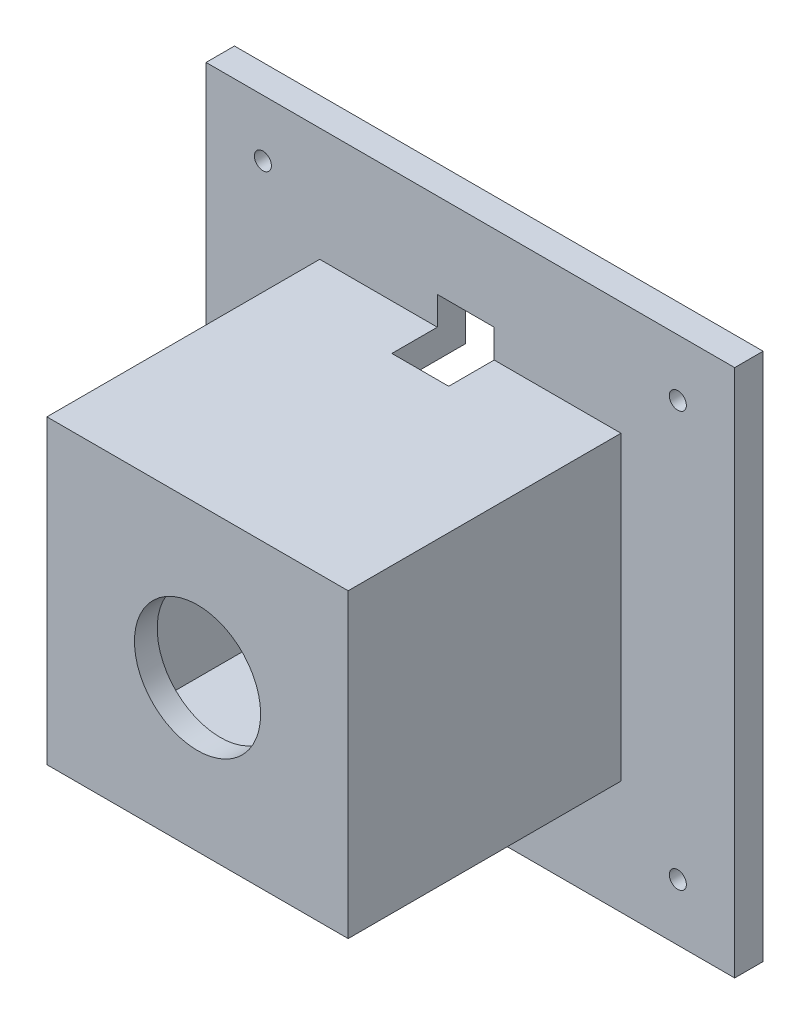
SolidWorks part; units mm, degrees
ref_plane "Plan de face" through (0, 0, 0) normal (0, 0, 1) x (1, 0, 0)
ref_plane "Plan de dessus" through (0, 0, 0) normal (0, 1, 0) x (1, 0, 0)
ref_plane "Plan de droite" through (0, 0, 0) normal (1, 0, 0) x (0, 0, -1)
sketch "Esquisse1" plane through (0, 0, 0) normal (0, 0, 1) x (1, 0, 0)
  line L1 (-21.4803, 20.2237) -> (71.5197, 20.2237)
  line L2 (-21.4803, 20.2237) -> (-21.4803, -72.7763)
  line L3 (-21.4803, -72.7763) -> (71.5197, -72.7763)
  line L4 (71.5197, 20.2237) -> (71.5197, -72.7763)
  dimension "D1" = 93
  dimension "D2" = 93
extrude "Boss.-Extru.1" add sketch "Esquisse1" along normal blind 5
sketch "Esquisse2" plane through (0, 0, 5) normal (0, 0, 1) x (1, 0, 0)
  line L0 (-21.4803, 20.2237) -> (71.5197, -72.7763) construction
  line L1 (71.5197, -72.7763) -> (71.5197, 20.2237) construction
  line L2 (71.5197, 20.2237) -> (-21.4803, -72.7763) construction
  line L4 (-1.4803, 0.2237) -> (51.5197, 0.2237)
  line L5 (-1.4803, 0.2237) -> (-1.4803, -52.7763)
  line L6 (-1.4803, -52.7763) -> (51.5197, -52.7763)
  line L7 (51.5197, 0.2237) -> (51.5197, -52.7763)
  dimension "D1" = 53
  dimension "D2" = 53
extrude "Boss.-Extru.2" add sketch "Esquisse2" along normal blind 48
sketch "Esquisse3" plane through (0, 0, 0) normal (0, 0, -1) x (-1, 0, 0)
  line L8 (21.4803, 20.2237) -> (-71.5197, -72.7763) construction
  line L9 (-46.5197, -47.7763) -> (-3.5197, -47.7763)
  line L10 (-46.5197, -47.7763) -> (-46.5197, -4.7763)
  line L11 (-46.5197, -4.7763) -> (-3.5197, -4.7763)
  line L12 (-3.5197, -47.7763) -> (-3.5197, -4.7763)
  line L13 (-46.5197, -47.7763) -> (-3.5197, -4.7763) construction
  line L14 (-46.5197, -4.7763) -> (-3.5197, -47.7763) construction
  point P0 (-25.0197, -26.2763)
  dimension "D1" = 43
  dimension "D2" = 43
extrude "Enlèv. mat.-Extru.1" cut sketch "Esquisse3" against normal blind 49
sketch "Esquisse4" plane through (0, 0, 53) normal (0, 0, 1) x (1, 0, 0)
  line L0 (51.5197, 0.2237) -> (-1.4803, -52.7763) construction
  line L1 (-1.4803, 0.2237) -> (-1.4803, -52.7763) construction
  line L2 (-1.4803, -52.7763) -> (51.5197, -52.7763) construction
  line L3 (51.5197, -52.7763) -> (-1.4803, 0.2237) construction
  circle A0 centre (25.0197, -26.2763) radius 11.1
  dimension "D1" = 22.2
extrude "Enlèv. mat.-Extru.2" cut sketch "Esquisse4" against normal up to next
sketch "Esquisse5" plane through (0, 0, 5) normal (0, 0, 1) x (1, 0, 0)
  line L0 (71.5197, -72.7763) -> (-21.4803, 20.2237) construction
  line L1 (-21.4803, 20.2237) -> (-21.4803, -72.7763) construction
  line L2 (-21.4803, -72.7763) -> (71.5197, 20.2237) construction
  line L3 (-21.4803, -72.7763) -> (71.5197, -72.7763) construction
  line L4 (71.5197, -72.7763) -> (71.5197, 20.2237) construction
  circle A0 centre (61.5197, -62.7763) radius 1.5
  circle A1 centre (-11.4803, -62.7763) radius 1.5
  circle A2 centre (-11.4803, 10.2237) radius 1.5
  circle A3 centre (61.5197, 10.2237) radius 1.5
  dimension "D1" = 3
  dimension "D2" = 3
  dimension "D3" = 3
  dimension "D4" = 3
  dimension "D5" = 10
  dimension "D6" = 10
  dimension "D7" = 10
  dimension "D8" = 10
  dimension "D9" = 10
extrude "Enlèv. mat.-Extru.3" cut sketch "Esquisse5" against normal up to next
sketch "Esquisse7" plane through (0, -4.7763, 0) normal (0, -1, 0) x (1, 0, 0)
  line L0 (3.5197, 0) -> (46.5197, 0) construction
  line L1 (19.2073, 0) -> (29.2073, 0)
  line L2 (19.2073, 0) -> (19.2073, 13)
  line L3 (19.2073, 13) -> (29.2073, 13)
  line L4 (29.2073, 0) -> (29.2073, 13)
  dimension "D1" = 10
  dimension "D2" = 13
extrude "Enlèv. mat.-Extru.4" cut sketch "Esquisse7" against normal blind 10
